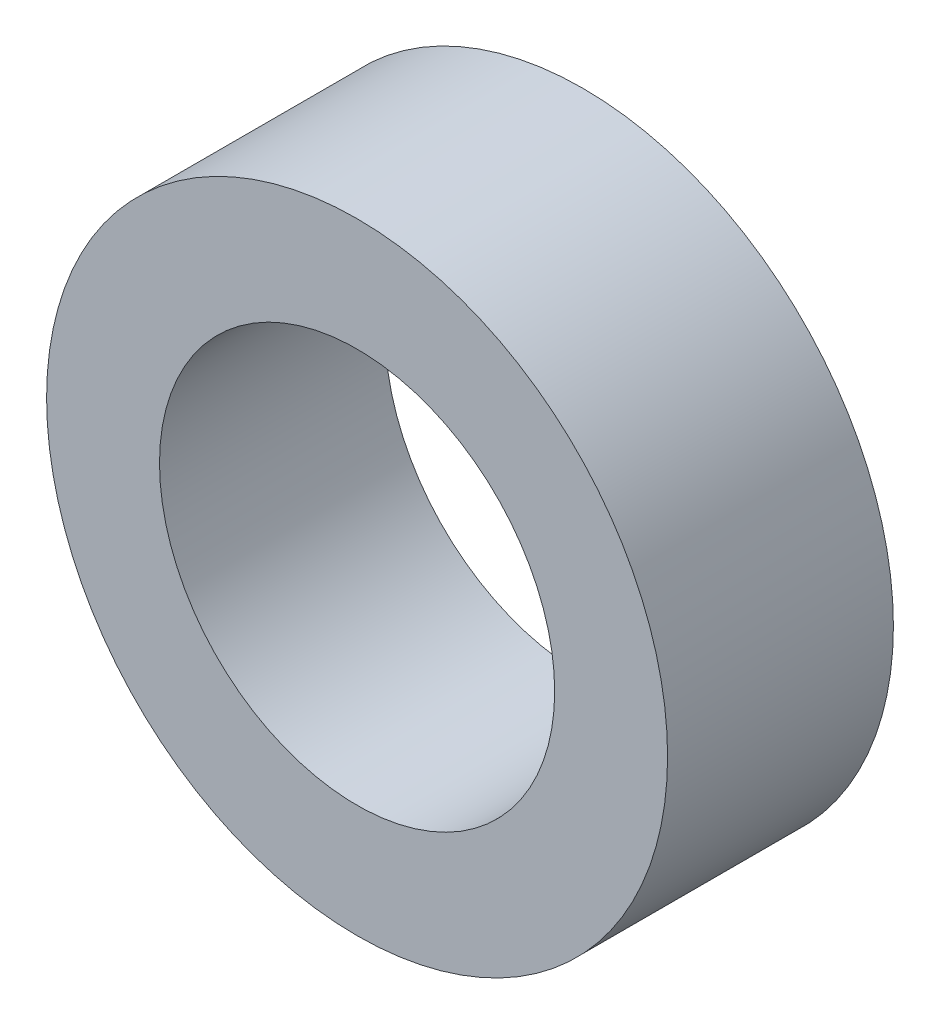
SolidWorks part; units mm, degrees
material "Natural Rubber"
ref_plane "Front Plane" through (0, 0, 0) normal (0, 0, 1) x (1, 0, 0)
ref_plane "Top Plane" through (0, 0, 0) normal (0, 1, 0) x (1, 0, 0)
ref_plane "Right Plane" through (0, 0, 0) normal (1, 0, 0) x (0, 0, -1)
sketch "Sketch1" plane through (0, 0, 0) normal (0, 0, 1) x (1, 0, 0)
  circle A0 centre (0, 0) radius 44
  circle A1 centre (0, 0) radius 28
  dimension "D1" = 88
  dimension "D2" = 56
extrude "Boss-Extrude1" add sketch "Sketch1" along normal blind 32
